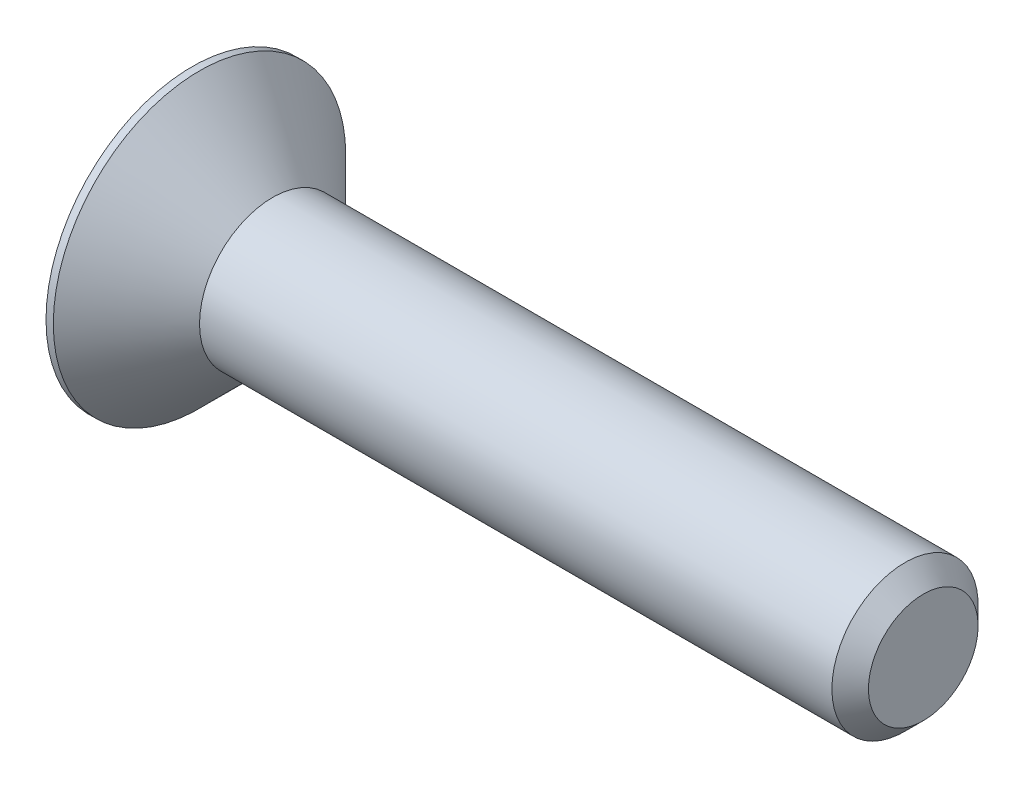
SolidWorks part; units mm, degrees
ref_plane "Front Plane" through (0, 0, 0) normal (0, 0, 1) x (1, 0, 0)
ref_plane "Top Plane" through (0, 0, 0) normal (0, 1, 0) x (1, 0, 0)
ref_plane "Right Plane" through (0, 0, 0) normal (1, 0, 0) x (0, 0, -1)
sketch "Sketch2" plane through (0, 0, 0) normal (0, 0, 1) x (1, 0, 0)
  line L0 (0, 0) -> (0, 2)
  line L1 (0, 2) -> (0.1, 2)
  line L2 (0.1, 2) -> (1.1, 1)
  line L3 (1.1, 1) -> (9.75, 1)
  line L4 (9.75, 1) -> (10, 0.75)
  line L5 (10, 0.75) -> (10, 0)
  line L6 (10, 0) -> (0, 0)
  line L7 (-2.2818, 0) -> (8.0811, 0) construction
  dimension "D1" = 4
  dimension "D2" = 0.1
  dimension "D3" = 45
  dimension "D4" = 10
  dimension "D5" = 0.25
  dimension "D6" = 2
revolve "Revolve1" add sketch "Sketch2" angle 360 about L7
sketch "Sketch3" plane through (0, 0, 0) normal (-1, 0, 0) x (0, 0, 1)
  line L1 (0.433, -0.75) -> (0.866, 0)
  line L2 (0.866, 0) -> (0.433, 0.75)
  line L3 (0.433, 0.75) -> (-0.433, 0.75)
  line L4 (-0.433, 0.75) -> (-0.866, 0)
  line L5 (-0.866, 0) -> (-0.433, -0.75)
  line L6 (-0.433, -0.75) -> (0.433, -0.75)
  circle A0 centre (0, 0) radius 0.75 construction
  dimension "D1" = 1.5
extrude "Cut-Extrude1" cut sketch "Sketch3" against normal blind 0.8
